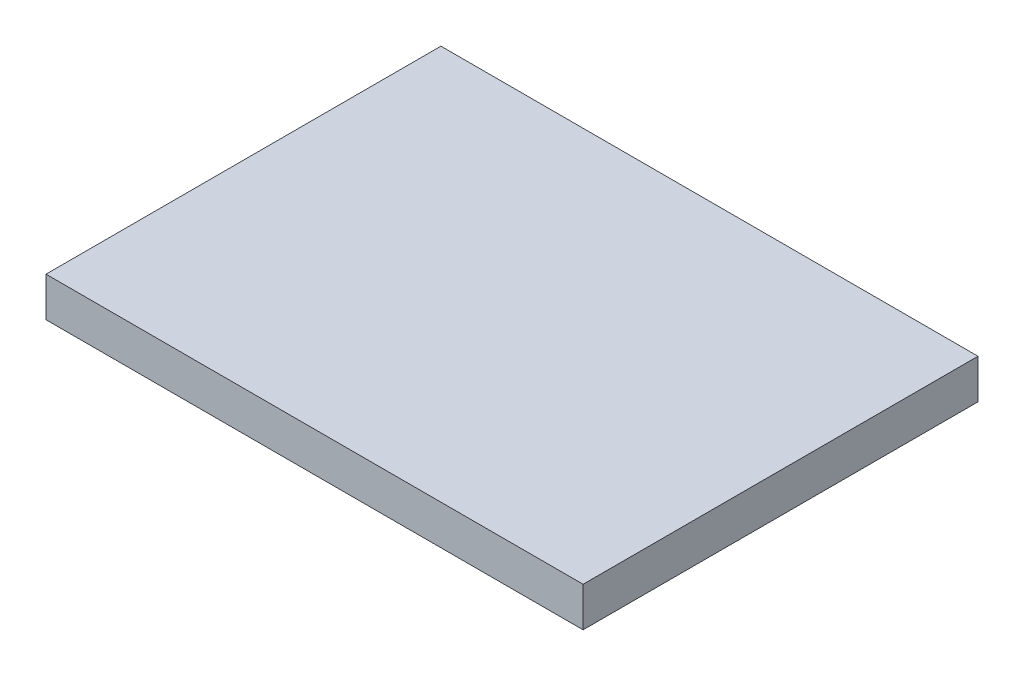
SolidWorks part; units mm, degrees
ref_plane "Front Plane" through (0, 0, 0) normal (0, 0, 1) x (1, 0, 0)
ref_plane "Top Plane" through (0, 0, 0) normal (0, 1, 0) x (1, 0, 0)
ref_plane "Right Plane" through (0, 0, 0) normal (1, 0, 0) x (0, 0, -1)
sketch "Sketch1" plane through (0, 0, 0) normal (0, 1, 0) x (1, 0, 0)
  line L1 (0, 0) -> (340, 0)
  line L2 (0, 0) -> (0, 250)
  line L3 (0, 250) -> (340, 250)
  line L4 (340, 0) -> (340, 250)
  dimension "D1" = 250
  dimension "D2" = 340
extrude "Boss-Extrude1" add sketch "Sketch1" along normal blind 25
